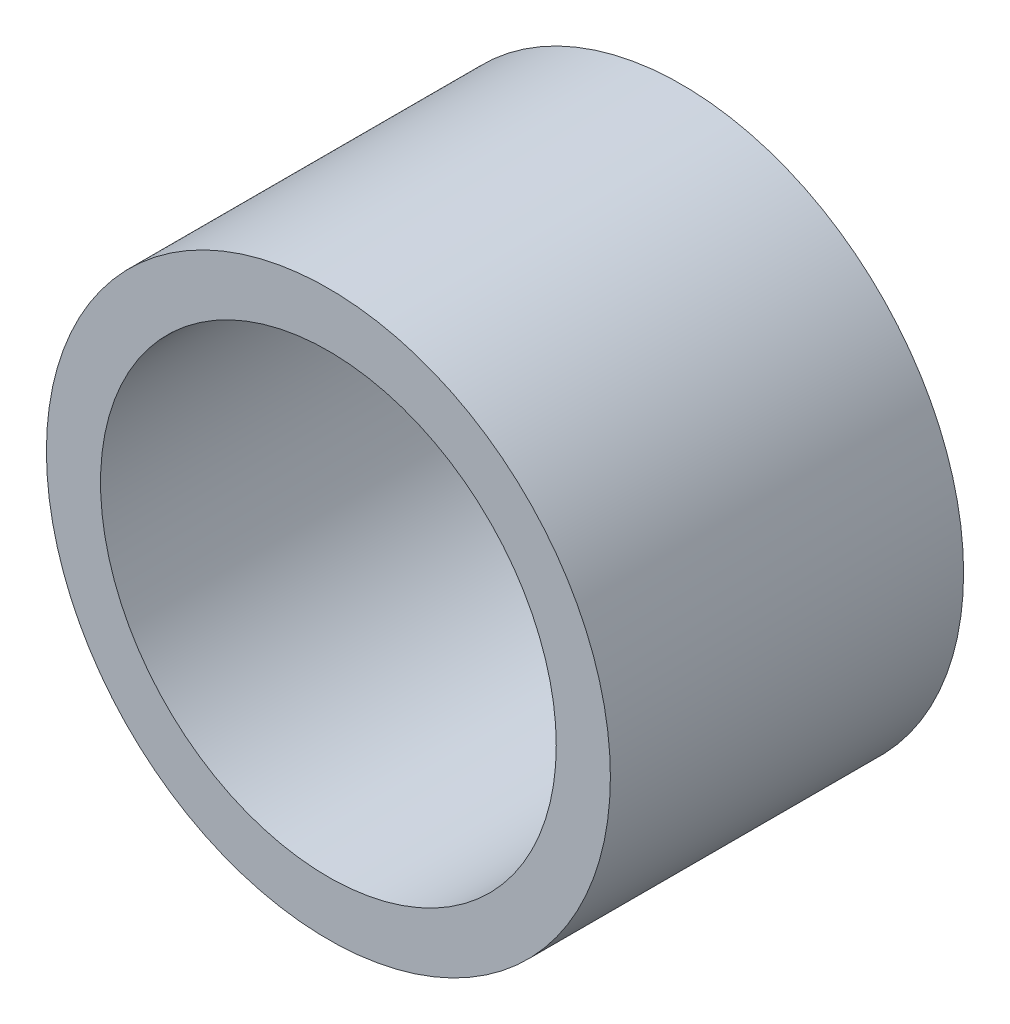
SolidWorks part; units mm, degrees
ref_plane "Front Plane" through (0, 0, 0) normal (0, 0, 1) x (1, 0, 0)
ref_plane "Top Plane" through (0, 0, 0) normal (0, 1, 0) x (1, 0, 0)
ref_plane "Right Plane" through (0, 0, 0) normal (1, 0, 0) x (0, 0, -1)
sketch "Sketch1" plane through (0, 0, 0) normal (0, 0, 1) x (1, 0, 0)
  circle A0 centre (0, 0) radius 6.2865
  circle A1 centre (0, 0) radius 5.08
  dimension "D1" = 12.573
  dimension "D2" = 10.16
extrude "Extrude1" add sketch "Sketch1" along normal blind 7.874
